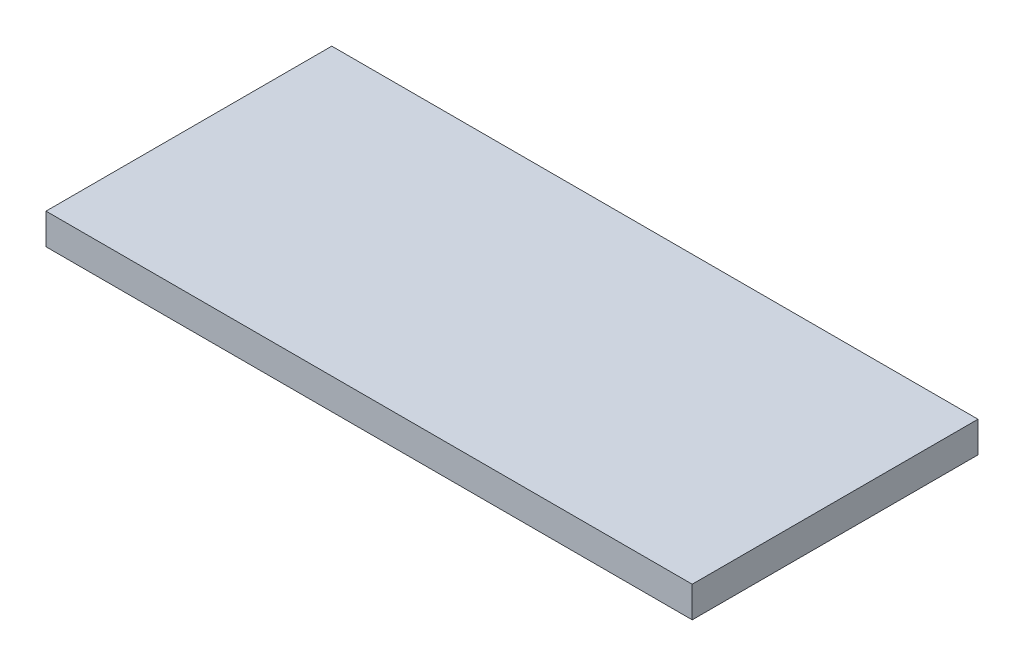
SolidWorks part; units mm, degrees
material "Maple"
ref_plane "Front Plane" through (0, 0, 0) normal (0, 0, 1) x (1, 0, 0)
ref_plane "Top Plane" through (0, 0, 0) normal (0, 1, 0) x (1, 0, 0)
ref_plane "Right Plane" through (0, 0, 0) normal (1, 0, 0) x (0, 0, -1)
sketch "Sketch1" plane through (0, 0, 0) normal (0, 1, 0) x (1, 0, 0)
  line L1 (-62.75, 27.75) -> (62.75, 27.75)
  line L2 (-62.75, 27.75) -> (-62.75, -27.75)
  line L3 (-62.75, -27.75) -> (62.75, -27.75)
  line L4 (62.75, 27.75) -> (62.75, -27.75)
  line L5 (-62.75, 27.75) -> (62.75, -27.75) construction
  line L6 (-62.75, -27.75) -> (62.75, 27.75) construction
  point P0 (0, 0)
  dimension "D1" = 55.5
  dimension "D2" = 125.5
extrude "Boss-Extrude1" add sketch "Sketch1" along normal blind 6
ref_plane "Plane1" through (0, 3, 0) normal (0, 1, 0) x (1, 0, 0)
